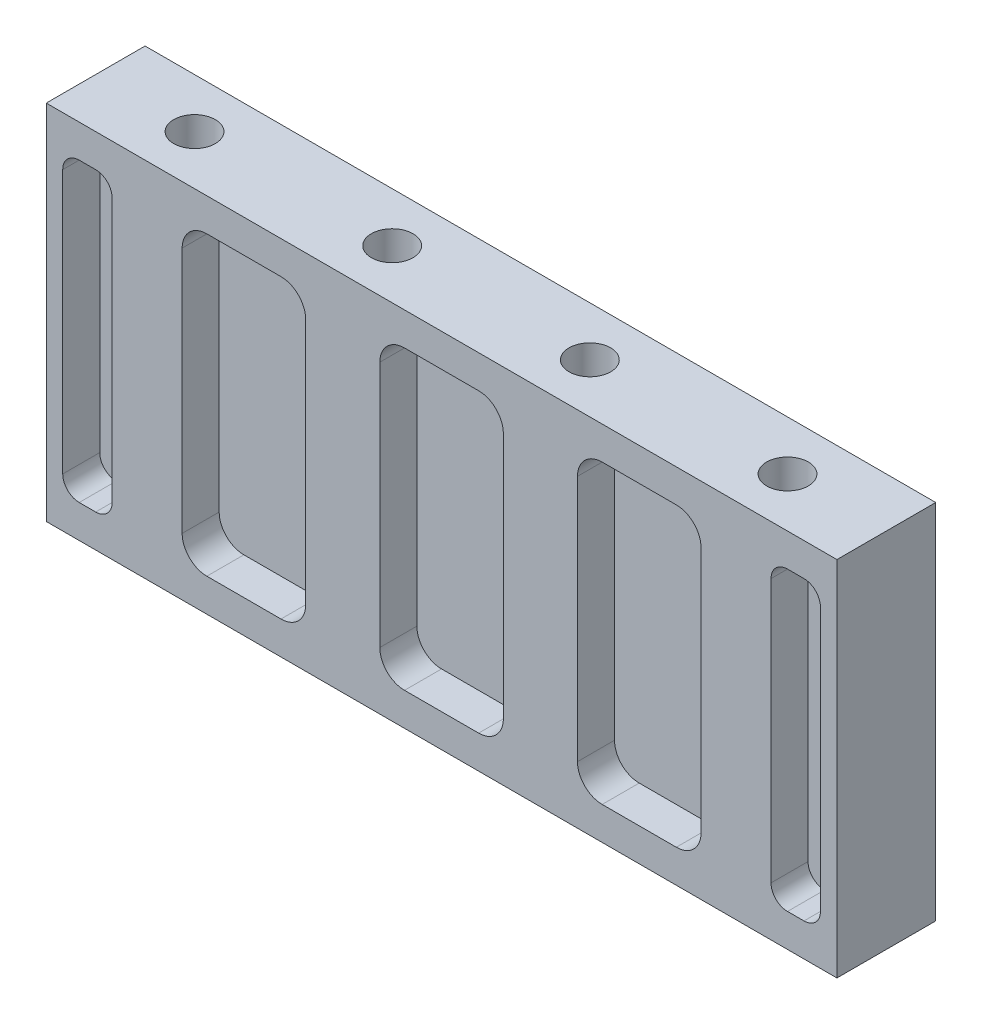
SolidWorks part; units mm, degrees
ref_plane "Front Plane" through (0, 0, 0) normal (0, 0, 1) x (1, 0, 0)
ref_plane "Top Plane" through (0, 0, 0) normal (0, 1, 0) x (1, 0, 0)
ref_plane "Right Plane" through (0, 0, 0) normal (1, 0, 0) x (0, 0, -1)
sketch "Sketch1" plane through (0, 0, 0) normal (0, 0, 1) x (1, 0, 0)
  line L1 (-76.2, 34.925) -> (76.2, 34.925)
  line L2 (-76.2, 34.925) -> (-76.2, -34.925)
  line L3 (-76.2, -34.925) -> (76.2, -34.925)
  line L4 (76.2, 34.925) -> (76.2, -34.925)
  line L5 (-76.2, 34.925) -> (76.2, -34.925) construction
  line L6 (-76.2, -34.925) -> (76.2, 34.925) construction
  point P0 (0, 0)
  dimension "D1" = 69.85
  dimension "D2" = 152.4
extrude "Boss-Extrude1" add sketch "Sketch1" along normal blind 19.05
sketch "Sketch2" plane through (0, 0, 19.05) normal (0, 0, 1) x (1, 0, 0)
  line L0 (-38.1, 0) -> (0, 0) construction
  line L1 (-45.2437, 28.575) -> (-30.9563, 28.575)
  line L2 (-50.0063, 23.8125) -> (-50.0063, -23.8125)
  line L3 (-45.2437, -28.575) -> (-30.9563, -28.575)
  line L4 (-26.1938, 23.8125) -> (-26.1938, -23.8125)
  line L5 (-50.0063, 28.575) -> (-26.1938, -28.575) construction
  line L6 (-50.0062, -28.575) -> (-26.1938, 28.575) construction
  line L7 (7.1437, 28.575) -> (-7.1437, 28.575)
  line L8 (11.9062, 23.8125) -> (11.9062, -23.8125)
  line L9 (7.1437, -28.575) -> (-7.1437, -28.575)
  line L10 (-11.9062, 23.8125) -> (-11.9062, -23.8125)
  line L11 (11.9062, 28.575) -> (-11.9062, -28.575) construction
  line L12 (11.9062, -28.575) -> (-11.9062, 28.575) construction
  line L13 (30.9563, 28.575) -> (45.2437, 28.575)
  line L14 (26.1938, 23.8125) -> (26.1938, -23.8125)
  line L15 (30.9563, -28.575) -> (45.2437, -28.575)
  line L16 (50.0063, 23.8125) -> (50.0063, -23.8125)
  line L17 (26.1938, 28.575) -> (50.0063, -28.575) construction
  line L18 (26.1938, -28.575) -> (50.0063, 28.575) construction
  line L19 (76.2, 34.925) -> (-76.2, 34.925) construction
  line L20 (68.2625, 0) -> (38.1, 0) construction
  line L21 (-69.85, 28.575) -> (-66.675, 28.575)
  line L22 (-73.025, 25.4) -> (-73.025, -25.4)
  line L23 (-69.85, -28.575) -> (-66.675, -28.575)
  line L24 (-63.5, 25.4) -> (-63.5, -25.4)
  line L25 (0, 0) -> (38.1, 0) construction
  line L26 (-73.025, 28.575) -> (-63.5, -28.575) construction
  line L27 (-73.025, -28.575) -> (-63.5, 28.575) construction
  line L28 (66.675, 28.575) -> (69.85, 28.575)
  line L29 (63.5, 25.4) -> (63.5, -25.4)
  line L30 (66.675, -28.575) -> (69.85, -28.575)
  line L31 (73.025, 25.4) -> (73.025, -25.4)
  line L32 (63.5, 28.575) -> (73.025, -28.575) construction
  line L33 (63.5, -28.575) -> (73.025, 28.575) construction
  line L34 (-68.2625, 0) -> (-38.1, 0) construction
  arc A0 (45.2437, -28.575) -> (50.0063, -23.8125) centre (45.2437, -23.8125) ccw
  arc A1 (45.2437, 28.575) -> (50.0063, 23.8125) centre (45.2437, 23.8125) cw
  arc A2 (30.9563, 28.575) -> (26.1938, 23.8125) centre (30.9563, 23.8125) ccw
  arc A3 (26.1938, -23.8125) -> (30.9563, -28.575) centre (30.9563, -23.8125) ccw
  arc A4 (11.9062, -23.8125) -> (7.1437, -28.575) centre (7.1437, -23.8125) cw
  arc A5 (7.1437, 28.575) -> (11.9062, 23.8125) centre (7.1437, 23.8125) cw
  arc A6 (-7.1437, 28.575) -> (-11.9062, 23.8125) centre (-7.1437, 23.8125) ccw
  arc A7 (-7.1437, -28.575) -> (-11.9062, -23.8125) centre (-7.1437, -23.8125) cw
  arc A8 (-50.0063, -23.8125) -> (-45.2437, -28.575) centre (-45.2437, -23.8125) ccw
  arc A9 (-30.9563, -28.575) -> (-26.1938, -23.8125) centre (-30.9563, -23.8125) ccw
  arc A10 (-30.9563, 28.575) -> (-26.1938, 23.8125) centre (-30.9563, 23.8125) cw
  arc A11 (-45.2437, 28.575) -> (-50.0063, 23.8125) centre (-45.2437, 23.8125) ccw
  arc A12 (66.675, 28.575) -> (63.5, 25.4) centre (66.675, 25.4) ccw
  arc A13 (69.85, 28.575) -> (73.025, 25.4) centre (69.85, 25.4) cw
  arc A14 (69.85, -28.575) -> (73.025, -25.4) centre (69.85, -25.4) ccw
  arc A15 (63.5, -25.4) -> (66.675, -28.575) centre (66.675, -25.4) ccw
  arc A16 (-73.025, -25.4) -> (-69.85, -28.575) centre (-69.85, -25.4) ccw
  arc A17 (-66.675, -28.575) -> (-63.5, -25.4) centre (-66.675, -25.4) ccw
  arc A18 (-66.675, 28.575) -> (-63.5, 25.4) centre (-66.675, 25.4) cw
  arc A19 (-69.85, 28.575) -> (-73.025, 25.4) centre (-69.85, 25.4) ccw
  point P0 (-38.1, 0)
  point P5 (0, 0)
  point P10 (38.1, 0)
  point P57 (-68.2625, 0)
  point P62 (68.2625, 0)
  dimension "D9" = 4.7625
  dimension "D16" = 3.175
  dimension "D1" = 38.1
  dimension "D2" = 38.1
  dimension "D3" = 23.8125
  dimension "D4" = 23.8125
  dimension "D5" = 23.8125
  dimension "D6" = 6.35
  dimension "D7" = 6.35
  dimension "D8" = 6.35
  dimension "D10" = 9.525
  dimension "D11" = 9.525
  dimension "D12" = 30.1625
  dimension "D13" = 30.1625
  dimension "D14" = 6.35
  dimension "D15" = 6.35
extrude "Cut-Extrude1" cut sketch "Sketch2" against normal blind 7.1374
sketch "Sketch3" plane through (0, 34.925, 0) normal (0, 1, 0) x (1, 0, 0)
  line L0 (57.15, -9.525) -> (19.05, -9.525) construction
  line L1 (19.05, -9.525) -> (-19.05, -9.525) construction
  line L2 (0, -9.525) -> (0, 0) construction
  line L3 (-19.05, -9.525) -> (-57.15, -9.525) construction
  line L4 (57.15, -9.525) -> (76.2, -9.525) construction
  line L5 (76.2, -19.05) -> (76.2, 0) construction
  circle A0 centre (-57.15, -9.525) radius 4.0132
  circle A1 centre (-19.05, -9.525) radius 4.0132
  circle A2 centre (19.05, -9.525) radius 4.0132
  circle A3 centre (57.15, -9.525) radius 4.0132
  dimension "D1" = 8.0264
  dimension "D2" = 38.1
  dimension "D3" = 38.1
  dimension "D4" = 38.1
extrude "Cut-Extrude2" cut sketch "Sketch3" against normal up to next
